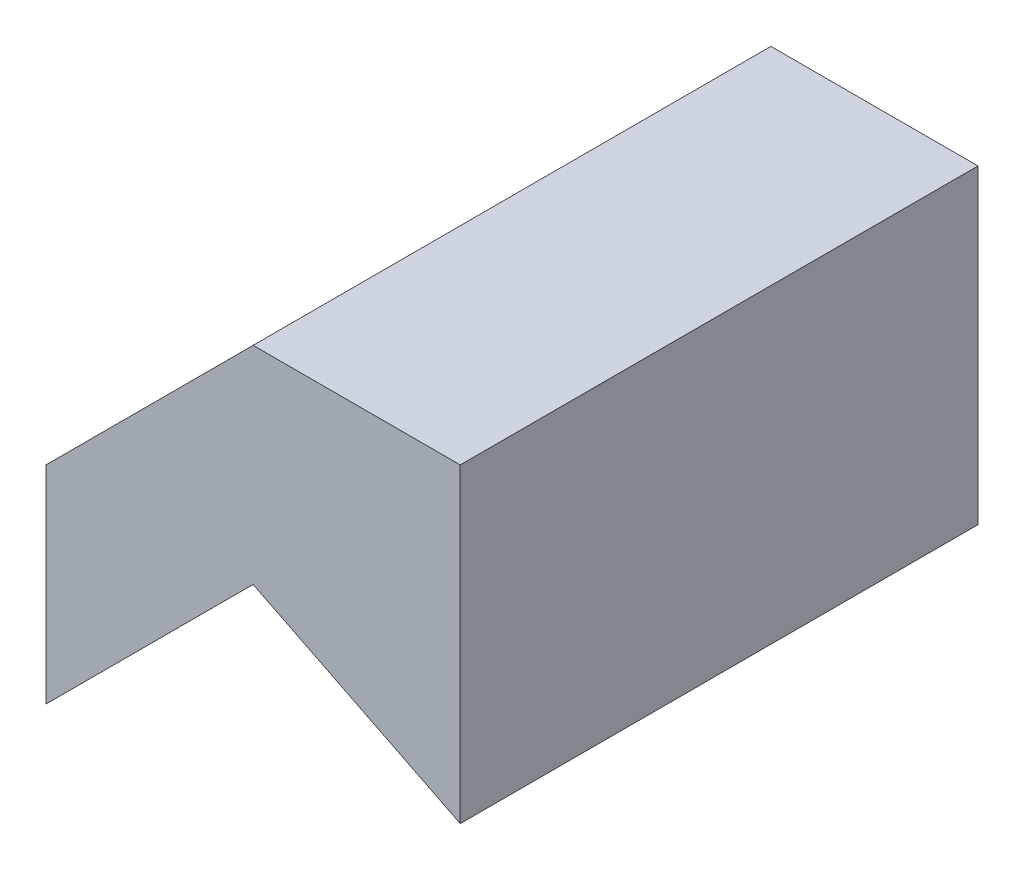
SolidWorks part; units mm, degrees
ref_plane "Front Plane" through (0, 0, 0) normal (0, 0, 1) x (1, 0, 0)
ref_plane "Top Plane" through (0, 0, 0) normal (0, 1, 0) x (1, 0, 0)
ref_plane "Right Plane" through (0, 0, 0) normal (1, 0, 0) x (0, 0, -1)
sketch "Sketch1" plane through (0, 0, 0) normal (0, 0, 1) x (1, 0, 0)
  line L0 (-10, 0) -> (0, 10)
  line L1 (0, 10) -> (10, 10)
  line L2 (10, 10) -> (10, -5)
  line L3 (10, -5) -> (0, 0)
  line L4 (0, 0) -> (-10, -10)
  line L5 (-10, -10) -> (-10, 0)
  dimension "D1" = 10
  dimension "D2" = 15
  dimension "D3" = 10
  dimension "D4" = 10
  dimension "D5" = 10
  dimension "D6" = 5
  dimension "D7" = 10
extrude "Boss-Extrude1" add sketch "Sketch1" along normal blind 25
